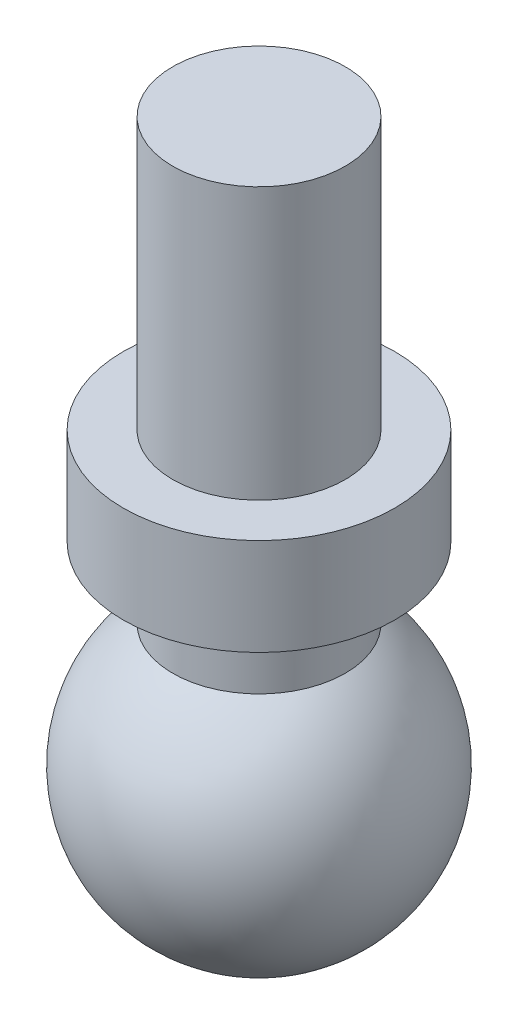
SolidWorks part; units mm, degrees
ref_plane "Front Plane" through (0, 0, 0) normal (0, 0, 1) x (1, 0, 0)
ref_plane "Top Plane" through (0, 0, 0) normal (0, 1, 0) x (1, 0, 0)
ref_plane "Right Plane" through (0, 0, 0) normal (1, 0, 0) x (0, 0, -1)
sketch "Sketch3" plane through (0, 0, 0) normal (0, 0, 1) x (1, 0, 0)
  line L0 (0, 1.9685) -> (0, -1.9685)
  arc A0 (0, 1.9685) -> (0, -1.9685) centre (0, 0) cw
revolve "Revolve1" add sketch "Sketch3" angle 360 about L0
ref_plane "Plane1" through (0, 0, 0) normal (0, 1, 0) x (-1, 0, 0)
sketch "Sketch4" plane through (0, 0, 0) normal (0, 1, 0) x (-1, 0, 0)
  circle A0 centre (0, 0) radius 1.1303
extrude "Extrude1" add sketch "Sketch4" along normal blind 7.366
ref_plane "Plane2" through (0, 2.54, 0) normal (0, 1, 0) x (-1, 0, 0)
sketch "Sketch5" plane through (0, 2.54, 0) normal (0, 1, 0) x (-1, 0, 0)
  circle A0 centre (0, 0) radius 1.778
extrude "Extrude2" add sketch "Sketch5" along normal blind 1.27
